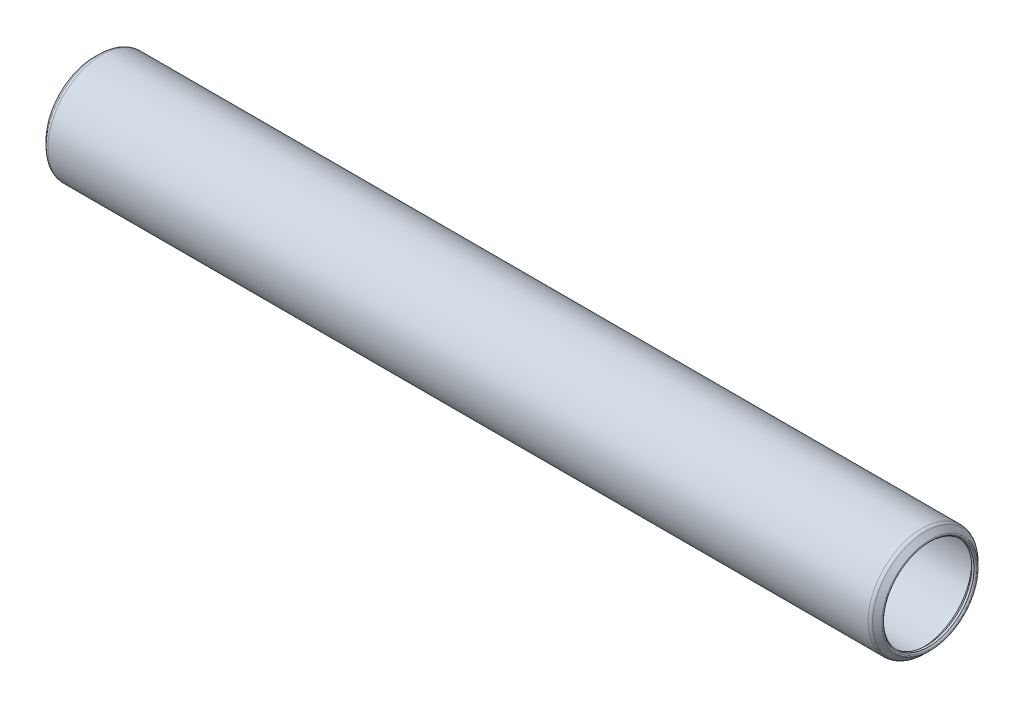
SolidWorks part; units mm, degrees
ref_plane "Front Plane" through (0, 0, 0) normal (0, 0, 1) x (1, 0, 0)
ref_plane "Top Plane" through (0, 0, 0) normal (0, 1, 0) x (1, 0, 0)
ref_plane "Right Plane" through (0, 0, 0) normal (1, 0, 0) x (0, 0, -1)
ref_plane "Plane1" through (0, 0, 0) normal (0, 0, 1) x (1, 0, 0)
sketch "Sketch1" plane through (0, 0, 0) normal (0, 0, 1) x (1, 0, 0)
  line L0 (-0.3964, 5.305) -> (-0.254, 5.1626)
  line L1 (-0.254, 5.1626) -> (0, 5.1626)
  line L2 (0, 5.1626) -> (0.508, 5.6705)
  line L3 (0.508, 5.6705) -> (93.9292, 5.6705)
  line L4 (93.9292, 5.6705) -> (94.4372, 5.1626)
  line L5 (94.4372, 5.1626) -> (94.6912, 5.1626)
  line L6 (94.6912, 5.1626) -> (94.8336, 5.305)
  line L7 (94.8336, 5.4846) -> (94.3011, 6.0171)
  line L8 (93.9419, 6.1658) -> (0.4953, 6.1658)
  line L9 (0.1361, 6.0171) -> (-0.3964, 5.4846)
  line L10 (94.4372, 0) -> (0, 0) construction
  arc A0 (-0.3964, 5.4846) -> (-0.3964, 5.305) centre (-0.3066, 5.3948) ccw
  arc A1 (94.8336, 5.305) -> (94.8336, 5.4846) centre (94.7438, 5.3948) ccw
  arc A2 (94.3011, 6.0171) -> (93.9419, 6.1658) centre (93.9419, 5.6578) ccw
  arc A3 (0.4953, 6.1658) -> (0.1361, 6.0171) centre (0.4953, 5.6578) ccw
revolve "Revolve1" add sketch "Sketch1" angle 360 about L10
